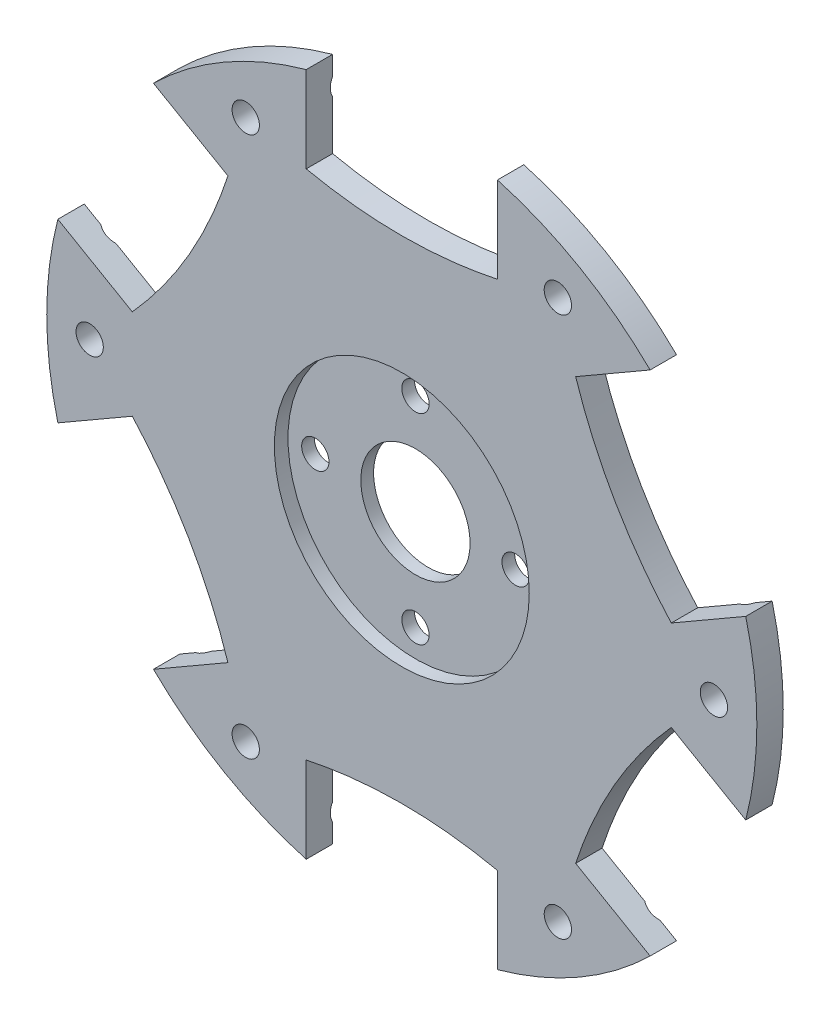
SolidWorks part; units mm, degrees
ref_plane "Alzado" through (0, 0, 0) normal (0, 0, 1) x (1, 0, 0)
ref_plane "Planta" through (0, 0, 0) normal (0, 1, 0) x (1, 0, 0)
ref_plane "Vista lateral" through (0, 0, 0) normal (1, 0, 0) x (0, 0, -1)
sketch "Croquis2" plane through (0, 0, 0) normal (0, 0, 1) x (1, 0, 0)
  line L0 (0, 0) -> (0, 41) construction
  line L1 (-9.5, 34.5) -> (9.5, 34.5) construction
  line L2 (0, 0) -> (41, 0) construction
  line L3 (-9.5, 29.1158) -> (-9.5, 39.8842) construction
  line L4 (9.5, 29.1158) -> (9.5, 39.8842) construction
  line L5 (-10.5, 37.56) -> (-10.5, 28.1158)
  line L6 (10.5, 37.56) -> (10.5, 28.1158)
  line L7 (27.2779, 27.8732) -> (19.099, 23.1512)
  line L8 (37.7779, 9.6867) -> (29.599, 4.9646)
  line L9 (37.7779, -9.6867) -> (29.599, -4.9646)
  line L10 (27.2779, -27.8732) -> (19.099, -23.1512)
  line L11 (10.5, -37.56) -> (10.5, -28.1158)
  line L12 (-10.5, -37.56) -> (-10.5, -28.1158)
  line L13 (-27.2779, -27.8732) -> (-19.099, -23.1512)
  line L14 (-37.7779, -9.6867) -> (-29.599, -4.9646)
  line L15 (-37.7779, 9.6867) -> (-29.599, 4.9646)
  line L16 (-27.2779, 27.8732) -> (-19.099, 23.1512)
  line L17 (10.5, 28.1158) -> (19.099, 23.1512) construction
  line L18 (0, 0) -> (17.892, 30.9899) construction
  circle A0 centre (0, 0) radius 41 construction
  circle A1 centre (0, 0) radius 39
  circle A2 centre (0, 0) radius 6
  circle A3 centre (0, 0) radius 35.7841 construction
  circle A5 centre (17.142, 29.6909) radius 1.5
  circle A6 centre (34.2841, 0) radius 1.5
  circle A7 centre (17.142, -29.6909) radius 1.5
  circle A8 centre (-17.142, -29.6909) radius 1.5
  circle A9 centre (-34.2841, 0) radius 1.5
  circle A10 centre (-17.142, 29.6909) radius 1.5
  spline S0 degree 2 poles (-9.5, 29.1158) (0, 26.8842) (9.5, 29.1158) knots 0 0 0 1 1 1 construction
  spline S1 degree 2 poles (-10.5, 28.1158) (0, 25.8842) (10.5, 28.1158) knots 0 0 0 1 1 1
  spline S2 degree 2 poles (19.099, 23.1512) (22.4164, 12.9421) (29.599, 4.9646) knots 0 0 0 1 1 1
  spline S3 degree 2 poles (29.599, -4.9646) (22.4164, -12.9421) (19.099, -23.1512) knots 0 0 0 1 1 1
  spline S4 degree 2 poles (10.5, -28.1158) (0, -25.8842) (-10.5, -28.1158) knots 0 0 0 1 1 1
  spline S5 degree 2 poles (-19.099, -23.1512) (-22.4164, -12.9421) (-29.599, -4.9646) knots 0 0 0 1 1 1
  spline S6 degree 2 poles (-29.599, 4.9646) (-22.4164, 12.9421) (-19.099, 23.1512) knots 0 0 0 1 1 1
  point P6 (0, 34.5)
  point P46 (14.7995, 25.6335)
  dimension "D1" = 82
  dimension "D4" = 78
  dimension "D10" = 12
  dimension "D11" = 3
  dimension "D12" = 6
  dimension "D2" = 34.5
  dimension "D3" = 19
  dimension "D5" = 6.5
  dimension "D6" = 1
  dimension "D7" = 1
  dimension "D8" = 1
  dimension "D9" = 6
extrude "Saliente-Extruir2" add sketch "Croquis2" along normal blind 2.9 contours S6 L15 A1 L14 S5 L13 L12 S4 L11 L10 S3 L9 L8 S2 L7 L6 S1 L5 L16 A10 A9 A8 A7 A6 A5 A2
sketch "Croquis4" plane through (0, 0, 0) normal (1, 0, 0) x (0, 0, -1)
  line L0 (0, 0) -> (0, 34.5) construction
  line L1 (0, 27.8732) -> (0, 37.56) construction
  line L2 (0, 0) -> (16.675, 0) construction
  line L3 (0, 34.5) -> (1.75, 34.5) construction
  circle A0 centre (1.75, 34.5) radius 2
  dimension "D2" = 4
  dimension "D1" = 1.75
  dimension "D3" = 34.5
extrude "Cortar-Extruir1" cut sketch "Croquis4" against normal mid plane 25
pattern_circular "MatrizC1" count 6 over 360 about axis through (0, 0, 0) along (0, 0, 1) of "Cortar-Extruir1"
sketch "Croquis5" plane through (0, 0, 2.9) normal (0, 0, 1) x (1, 0, 0)
  line L0 (0, 0) -> (11, 0) construction
  circle A0 centre (11, 0) radius 1.5
  circle A1 centre (0, -11) radius 1.5
  circle A2 centre (-11, 0) radius 1.5
  circle A3 centre (0, 11) radius 1.5
  point P13 (0, 0)
  dimension "D1" = 11
  dimension "D2" = 3
  dimension "D3" = 4
extrude "Cortar-Extruir2" cut sketch "Croquis5" against normal blind 10
sketch "Croquis6" plane through (0, 0, 2.9) normal (0, 0, 1) x (1, 0, 0)
  circle A0 centre (0, 0) radius 14
  dimension "D1" = 28
extrude "Cortar-Extruir3" cut sketch "Croquis6" against normal blind 1.5
